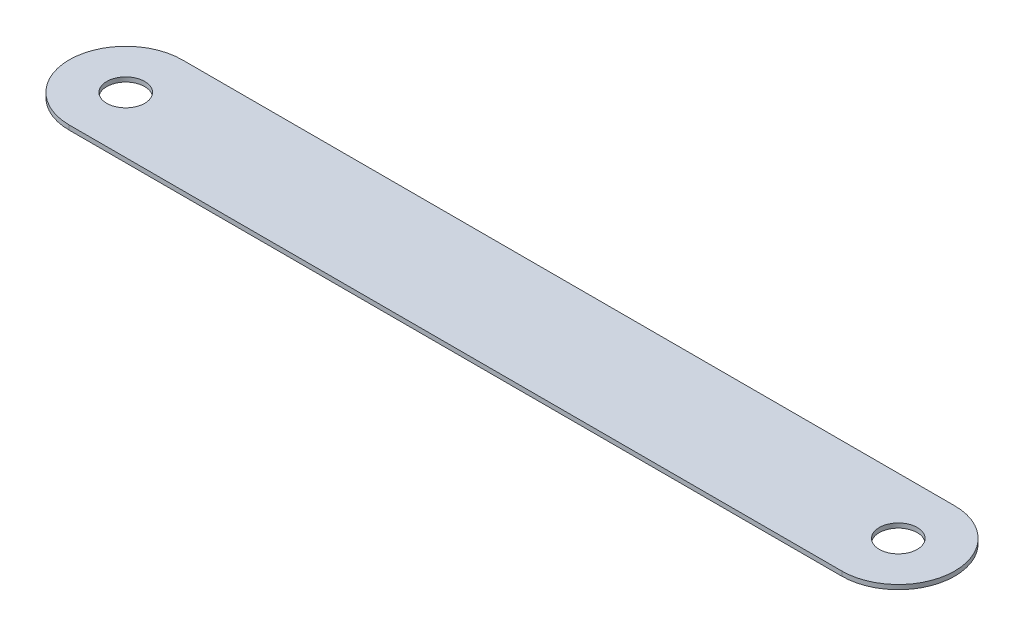
SolidWorks part; units mm, degrees
ref_plane "前基準面" through (0, 0, 0) normal (0, 0, 1) x (1, 0, 0)
ref_plane "上基準面" through (0, 0, 0) normal (0, 1, 0) x (1, 0, 0)
ref_plane "右基準面" through (0, 0, 0) normal (1, 0, 0) x (0, 0, -1)
sketch "草圖1" plane through (0, 0, 0) normal (0, 1, 0) x (1, 0, 0)
  line L0 (-42.75, 0) -> (42.75, 0) construction
  line L1 (-42.75, 6.25) -> (42.75, 6.25)
  line L2 (-42.75, -6.25) -> (42.75, -6.25)
  arc A0 (-42.75, 6.25) -> (-42.75, -6.25) centre (-42.75, 0) ccw
  arc A1 (42.75, -6.25) -> (42.75, 6.25) centre (42.75, 0) ccw
  circle A2 centre (-42.75, 0) radius 2.1
  circle A3 centre (42.75, 0) radius 2.1
  point P2 (0, 0)
  point P12 (-49, 0)
  point P13 (49, 0)
  dimension "D1" = 98
  dimension "D2" = 12.5
extrude "填料-伸長1" add sketch "草圖1" along normal blind 0.5
